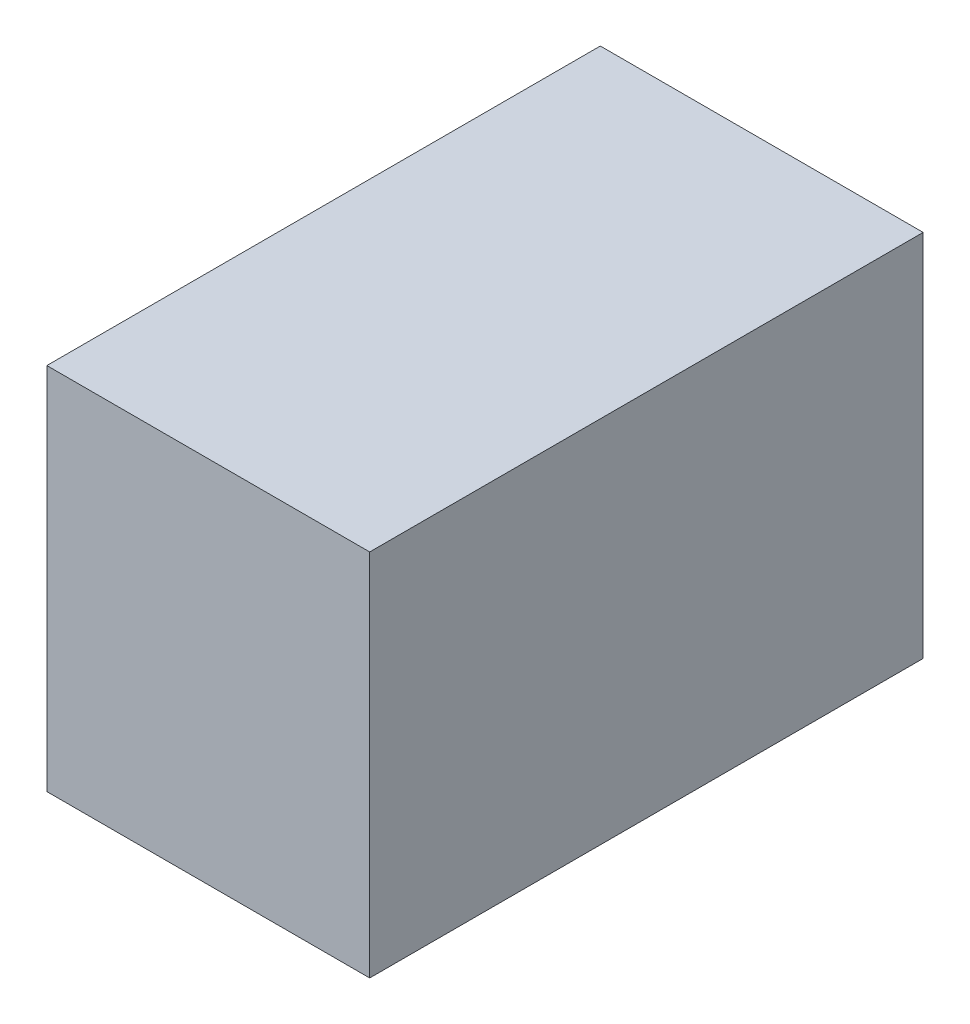
SolidWorks part; units mm, degrees
material "1023 al carbonio, lamiera (SS)"
ref_plane "Piano frontale" through (0, 0, 0) normal (0, 0, 1) x (1, 0, 0)
ref_plane "Piano superiore" through (0, 0, 0) normal (0, 1, 0) x (1, 0, 0)
ref_plane "Piano destro" through (0, 0, 0) normal (1, 0, 0) x (0, 0, -1)
sketch "Schizzo1" plane through (0, 0, 0) normal (0, 0, 1) x (1, 0, 0)
  line L0 (17.5, 40) -> (17.5, 0) construction
  line L1 (0, 0) -> (35, 0)
  line L2 (0, 0) -> (0, 40)
  line L3 (0, 40) -> (35, 40)
  line L4 (35, 0) -> (35, 40)
  dimension "D1" = 40
  dimension "D2" = 35
extrude "Estrusione-Estrusione1" add sketch "Schizzo1" along normal blind 60
